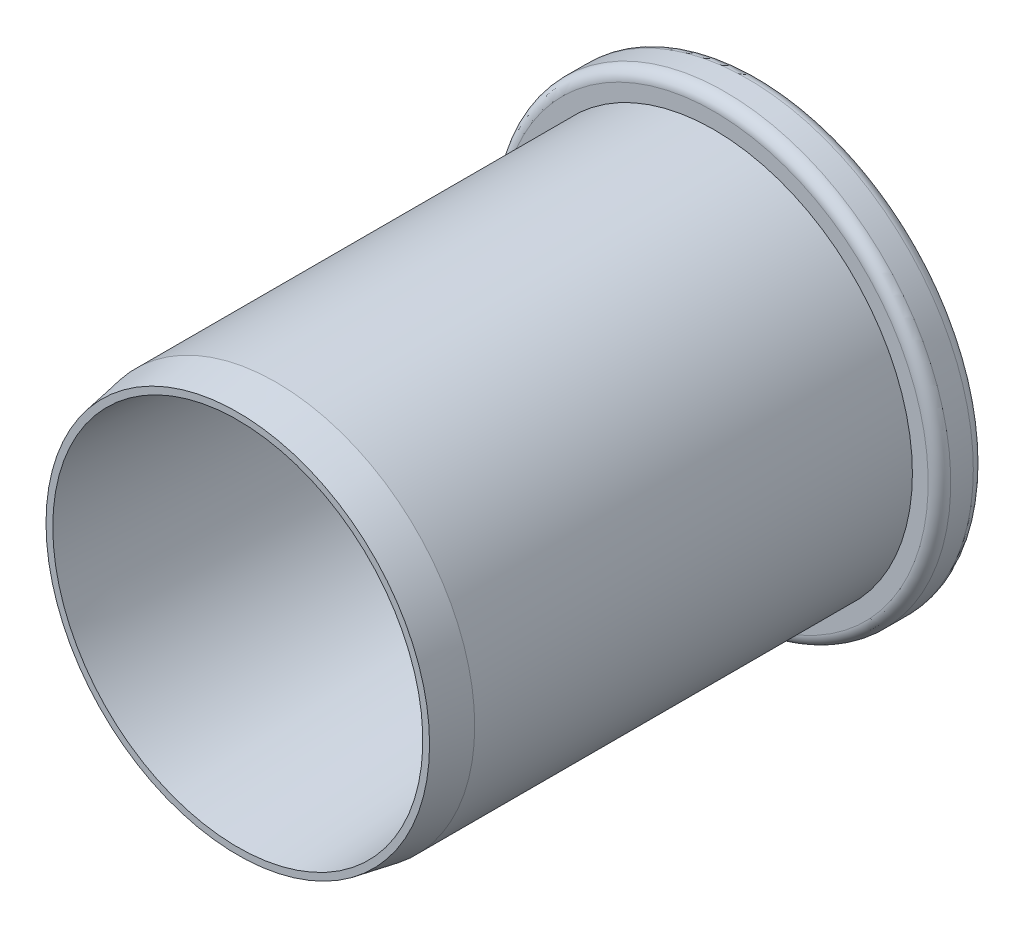
SolidWorks part; units mm, degrees
material "6061 Alloy"
ref_plane "Front" through (0, 0, 0) normal (0, 0, 1) x (1, 0, 0)
ref_plane "Top" through (0, 0, 0) normal (0, 1, 0) x (1, 0, 0)
ref_plane "Right" through (0, 0, 0) normal (1, 0, 0) x (0, 0, -1)
sketch "Sketch1" plane through (0, 0, 0) normal (0, 1, 0) x (1, 0, 0)
  line L0 (0, 0) -> (0, -62.3586) construction
  line L1 (5, 0) -> (10, 0)
  line L2 (10, 0) -> (10, -2)
  line L3 (10, -2) -> (8.8, -2)
  line L4 (8.8, -2) -> (8.8, -10)
  line L5 (3.2367, -10) -> (7.3, -10)
  line L6 (5, 0) -> (3.2367, -10)
  line L7 (8.8, -10) -> (8.8, -21.3986)
  line L8 (8.8, -21.3986) -> (8.5, -23.1)
  line L9 (8.5, -23.1) -> (8.2, -23.1)
  line L10 (8.2, -23.1) -> (7.3, -10)
  dimension "D1" = 10
  dimension "D2" = 17.6
  dimension "D3" = 100
  dimension "D4" = 2
  dimension "D5" = 20
  dimension "D6" = 10
  dimension "D7" = 1.5
  dimension "D8" = 0.3
  dimension "D9" = 0.3
  dimension "D10" = 13.1
revolve "Revolve1" add sketch "Sketch1" angle 360 about L0
fillet "Fillet1" radius 0.5 3 edges at (-5, 0, 0) (-10, 0, 2) (-10, 0, 0)
